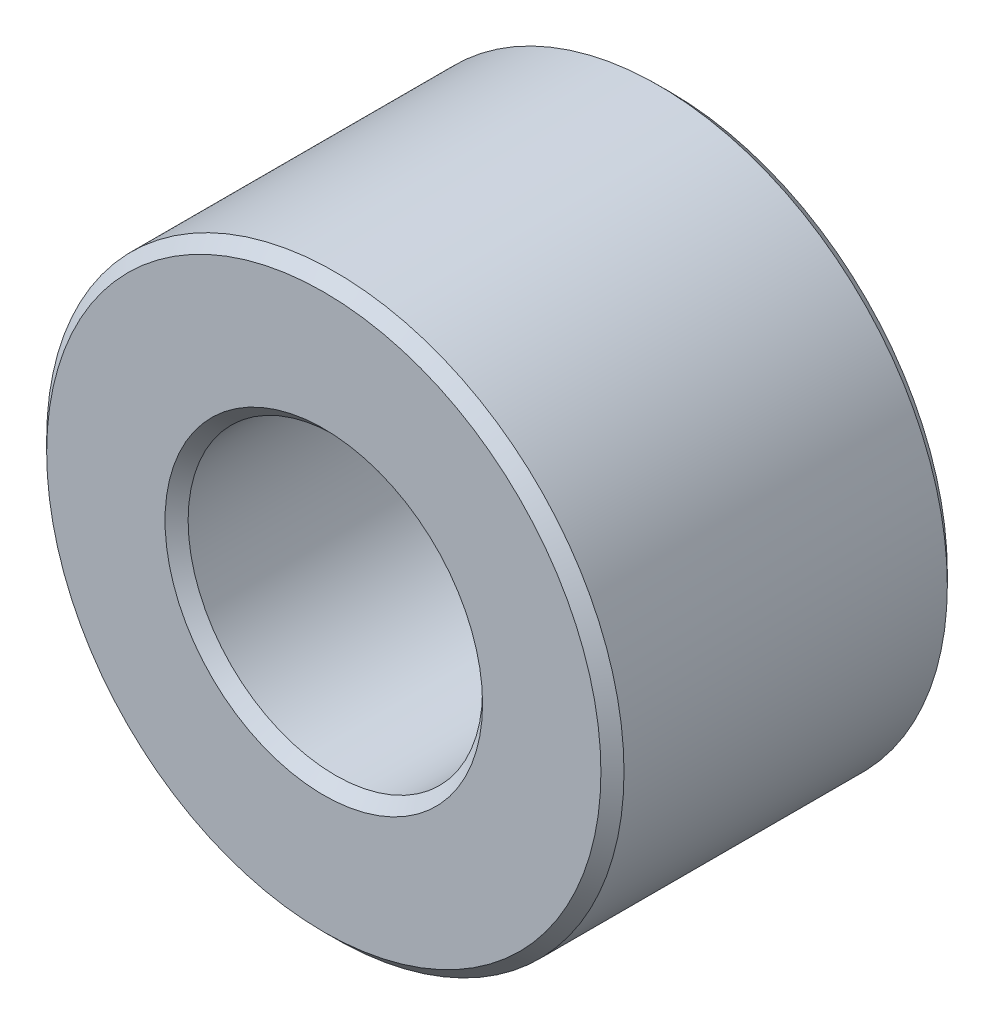
SolidWorks part; units mm, degrees
material "6061-T6 (SS)"
ref_plane "Front Plane" through (0, 0, 0) normal (0, 0, 1) x (1, 0, 0)
ref_plane "Top Plane" through (0, 0, 0) normal (0, 1, 0) x (1, 0, 0)
ref_plane "Right Plane" through (0, 0, 0) normal (1, 0, 0) x (0, 0, -1)
sketch "Sketch1" plane through (0, 0, 0) normal (0, 0, 1) x (1, 0, 0)
  circle A0 centre (0, 0) radius 2.55
  circle A1 centre (0, 0) radius 5
  dimension "D1" = 5.1
  dimension "D2" = 10
extrude "Boss-Extrude1" add sketch "Sketch1" along normal blind 6
chamfer "Chamfer1" distance 0.2 angle 45 4 edges at (5, 0, 0) (2.55, 0, 0) (2.55, 0, 6) (5, 0, 6)
move or copy body "Sólido-Mover/Copiar1" [suppressed] bodies to move or copy 101
